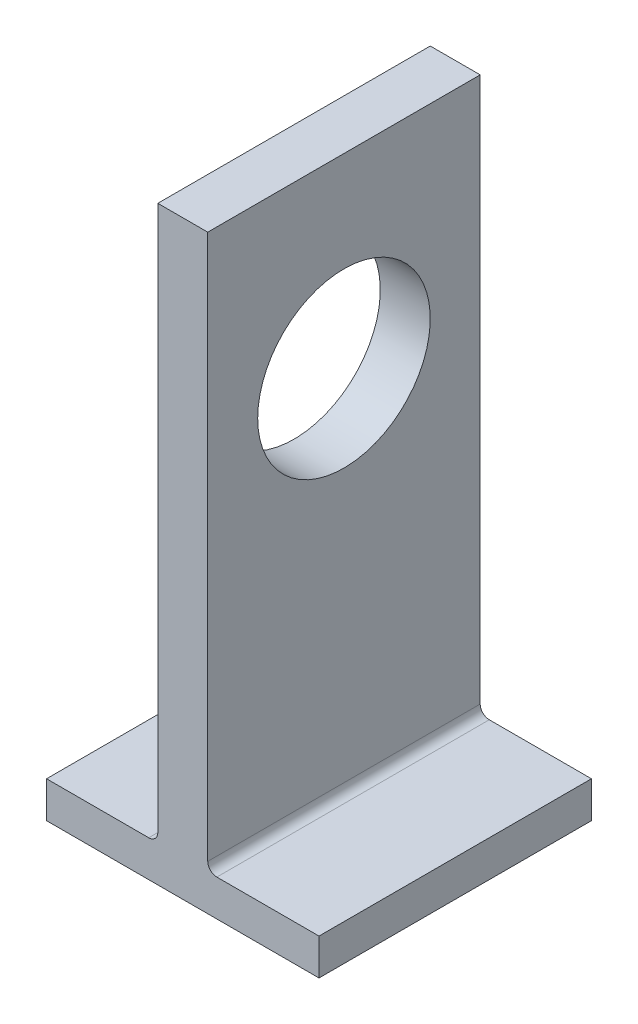
SolidWorks part; units mm, degrees
ref_plane "Front Plane" through (0, 0, 0) normal (0, 0, 1) x (1, 0, 0)
ref_plane "Top Plane" through (0, 0, 0) normal (0, 1, 0) x (1, 0, 0)
ref_plane "Right Plane" through (0, 0, 0) normal (1, 0, 0) x (0, 0, -1)
sketch "Sketch1" plane through (0, 0, 0) normal (0, 0, 1) x (1, 0, 0)
  line L0 (3.75, 0) -> (15, 0)
  line L1 (-15, 0) -> (-3.75, 0)
  line L2 (-15, 0) -> (-15, -4)
  line L3 (-15, -4) -> (15, -4)
  line L4 (15, 0) -> (15, -4)
  line L6 (-2.75, 1) -> (-2.75, 61)
  line L7 (-2.75, 61) -> (2.75, 61)
  line L8 (2.75, 1) -> (2.75, 61)
  line L9 (-3.9306, -0.1355) -> (-3.9169, 0) construction
  line L11 (2.8325, 0) -> (2.8463, -0.1355) construction
  arc A0 (-3.75, 0) -> (-2.75, 1) centre (-3.75, 1) ccw
  arc A1 (3.75, 0) -> (2.75, 1) centre (3.75, 1) cw
  point P4 (-0.5422, 33.2071)
  point P17 (0, -4)
  point P19 (0, 61)
  dimension "D1" = 1
  dimension "D2" = 1
  dimension "D3" = 60
  dimension "D4" = 30
  dimension "D5" = 5.5
  dimension "D6" = 4
extrude "Boss-Extrude1" add sketch "Sketch1" along normal blind 30
sketch "Sketch2" plane through (-2.75, 0, 0) normal (-1, 0, 0) x (0, 0, 1)
  line L1 (30, 0) -> (0, 0) construction
  line L2 (30, 61) -> (0, 61) construction
  circle A0 centre (15, 40.5) radius 9.5
  point P2 (0, 0)
  point P7 (15, 61)
  dimension "D1" = 19
  dimension "D2" = 40.5
extrude "Cut-Extrude1" cut sketch "Sketch2" against normal blind 70
